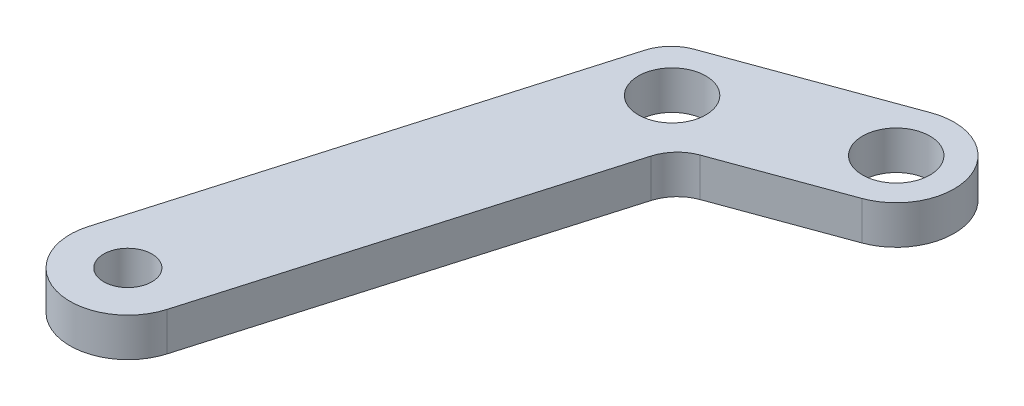
SolidWorks part; units mm, degrees
ref_plane "Front Plane" through (0, 0, 0) normal (0, 0, 1) x (1, 0, 0)
ref_plane "Top Plane" through (0, 0, 0) normal (0, 1, 0) x (1, 0, 0)
ref_plane "Right Plane" through (0, 0, 0) normal (1, 0, 0) x (0, 0, -1)
sketch "Sketch1" plane through (0, 0, 0) normal (0, 1, 0) x (1, 0, 0)
  line L0 (-10609.3809, 26644.2754) -> (-10602.5942, 26667.5816)
  line L1 (-10602.5942, 26667.5816) -> (-10592.6608, 26671.2131)
  line L3 (-10603.6201, 26642.5979) -> (-10597.6823, 26662.9889)
  line L4 (-10597.6823, 26662.9889) -> (-10590.6007, 26665.5778)
  line L5 (-10609.3809, 26644.2754) -> (-10603.6201, 26642.5979) construction
  line L6 (-10597.6823, 26662.9889) -> (-10602.5942, 26667.5816) construction
  line L7 (-10590.6007, 26665.5778) -> (-10592.6608, 26671.2131) construction
  arc A0 (-10592.6608, 26671.2131) -> (-10590.6007, 26665.5778) centre (-10591.6307, 26668.3954) cw
  arc A1 (-10609.3809, 26644.2754) -> (-10603.6201, 26642.5979) centre (-10606.5005, 26643.4366) ccw
  circle A3 centre (-10591.6307, 26668.3954) radius 1.75
  circle A4 centre (-10600.1383, 26665.2852) radius 1.75
  circle A5 centre (-10606.5005, 26643.4366) radius 1.25
  point P12 (-10591.6307, 26668.3954)
  point P13 (-10600.1383, 26665.2852)
  point P16 (-10606.5005, 26643.4366)
  dimension "D1" = 2.5
  dimension "D2" = 3.5
  dimension "D3" = 6
  dimension "D4" = 6.3622
  dimension "D5" = 8.5075
  dimension "D6" = 6
  dimension "D13" = 22.7561
  dimension "D14" = 9.0582
extrude "Boss-Extrude1" add sketch "Sketch1" along normal blind 2
fillet "Fillet1" radius 2 2 edges at (-10602.5942, 1, -26667.5816) (-10597.6823, 1, -26662.9889)
